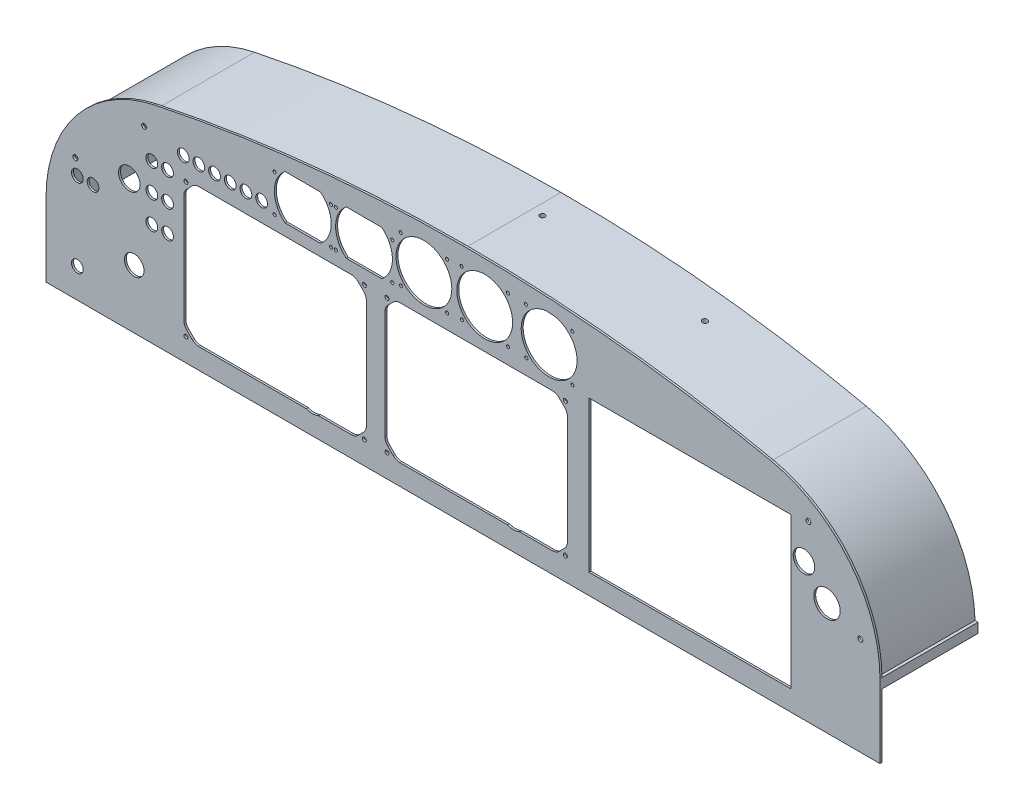
SolidWorks part; units mm, degrees
ref_plane "Front Plane" through (0, 0, 0) normal (0, 0, 1) x (1, 0, 0)
ref_plane "Top Plane" through (0, 0, 0) normal (0, 1, 0) x (1, 0, 0)
ref_plane "Right Plane" through (0, 0, 0) normal (1, 0, 0) x (0, 0, -1)
sketch "Sketch1" plane through (0, 0, 0) normal (0, 0, 1) x (1, 0, 0)
  line L7 (649.4412, 140.3074) -> (649.4412, 155.3074)
  line L9 (649.4412, 155.3074) -> (649.4412, 215.3074)
  line L39 (1500.4412, 215.3074) -> (1500.4412, 140.3074)
  line L40 (1500.4412, 140.3074) -> (649.4412, 140.3074)
  line L62 (1195.3999, 329.0734) -> (1195.3999, 146.8734) construction
  line L63 (1195.3999, 146.8734) -> (1417.5999, 146.8734) construction
  line L64 (1417.5999, 146.8734) -> (1417.5999, 329.0734) construction
  line L65 (1417.5999, 329.0734) -> (1195.3999, 329.0734) construction
  line L66 (1203.4999, 314.9734) -> (1203.4999, 160.9734)
  line L67 (1203.4999, 160.9734) -> (1409.4999, 160.9734)
  line L68 (1409.4999, 160.9734) -> (1409.4999, 314.9734)
  line L69 (1409.4999, 314.9734) -> (1203.4999, 314.9734)
  line L70 (1132.5647, 161.3083) -> (1166.0597, 161.3083)
  line L71 (1003.7003, 164.2372) -> (998.2444, 169.6931)
  line L72 (995.3155, 176.7641) -> (995.3155, 287.2524)
  line L73 (998.2444, 294.3235) -> (1003.7003, 299.7794)
  line L74 (1010.7714, 302.7083) -> (1166.0597, 302.7083)
  line L75 (1173.1307, 299.7794) -> (1178.5866, 294.3235)
  line L76 (1181.5155, 287.2524) -> (1181.5155, 176.7641)
  line L77 (1178.5866, 169.6931) -> (1173.1307, 164.2372)
  line L78 (1120.2663, 161.3083) -> (1010.7714, 161.3083)
  line L79 (989.0155, 303.7083) -> (989.0155, 160.3083) construction
  line L80 (994.0155, 155.3083) -> (1182.8155, 155.3083) construction
  line L81 (1187.8155, 160.3083) -> (1187.8155, 303.7083) construction
  line L82 (1182.8155, 308.7083) -> (994.0155, 308.7083) construction
  line L83 (927.3972, 161.3083) -> (960.8921, 161.3083)
  line L84 (798.5328, 164.2372) -> (793.0769, 169.6931)
  line L85 (790.148, 176.7641) -> (790.148, 287.2524)
  line L86 (793.0769, 294.3235) -> (798.5328, 299.7794)
  line L87 (805.6038, 302.7083) -> (960.8921, 302.7083)
  line L88 (967.9632, 299.7794) -> (973.419, 294.3235)
  line L89 (976.348, 287.2524) -> (976.348, 176.7641)
  line L90 (973.419, 169.6931) -> (967.9632, 164.2372)
  line L91 (915.0988, 161.3083) -> (805.6038, 161.3083)
  line L92 (783.848, 303.7083) -> (783.848, 160.3083) construction
  line L93 (788.848, 155.3083) -> (977.648, 155.3083) construction
  line L94 (982.648, 160.3083) -> (982.648, 303.7083) construction
  line L95 (977.648, 308.7083) -> (788.848, 308.7083) construction
  line L96 (1138.8693, 326.2789) -> (1135.2791, 322.6546)
  line L97 (1143.7303, 314.2034) -> (1147.3546, 317.7936)
  line L98 (1073.1573, 327.1493) -> (1069.5671, 323.525)
  line L99 (1078.0183, 315.0738) -> (1081.6426, 318.664)
  line L100 (1011.0893, 326.0184) -> (1007.4991, 322.3941)
  line L101 (1015.9503, 313.9429) -> (1019.5746, 317.5331)
  line L104 (955.8937, 360.0074) -> (991.9886, 360.0074)
  line L105 (955.8937, 314.6074) -> (991.9886, 314.6074)
  line L106 (893.3937, 360.0074) -> (929.4886, 360.0074)
  line L107 (893.3937, 314.6074) -> (929.4886, 314.6074)
  line L108 (670.7329, 250.3074) -> (707.3563, 250.3074) construction
  line L109 (669.6858, 170.3074) -> (692.7137, 170.3074) construction
  line L110 (724.2442, 200.3074) -> (757.1244, 200.3074) construction
  line L111 (739.7591, 245.3074) -> (779.4653, 245.3074) construction
  line L112 (745.1465, 273.3074) -> (781.6369, 273.3074) construction
  line L113 (742.3123, 301.3074) -> (779.4412, 301.3074) construction
  line L114 (779.1244, 322.3074) -> (878.3543, 322.3074) construction
  line L115 (863.5551, 337.3074) -> (1002.9412, 337.3074) construction
  line L116 (911.4412, 368.3649) -> (911.4412, 302.7083) construction
  line L117 (973.9412, 366.2956) -> (973.9412, 308.7083) construction
  line L118 (1035.0328, 379.7186) -> (1035.0328, 308.7083) construction
  line L119 (1097.1009, 379.7186) -> (1097.1009, 308.7083) construction
  line L120 (1162.8129, 379.7186) -> (1162.8129, 308.7083) construction
  line L121 (1006.5328, 341.4767) -> (1195.3999, 341.4767) construction
  circle A4 centre (853.4412, 322.3074) radius 6
  circle A48 centre (869.4412, 322.3074) radius 6
  arc A52 (649.4412, 215.3074) -> (760.4161, 352.2656) centre (789.4412, 215.3074) cw
  arc A53 (760.4161, 352.2656) -> (1074.9412, 385.3074) centre (1075.704, -1135.4566) cw
  arc A54 (1074.9412, 385.3074) -> (1389.4663, 352.2656) centre (1075.6967, -1121.0041) cw
  arc A55 (1389.4663, 352.2656) -> (1500.4412, 215.3074) centre (1360.2677, 215.1668) cw
  circle A62 centre (997.3655, 163.6583) radius 2.032
  circle A101 centre (1179.4655, 163.6583) radius 2.032
  circle A102 centre (1179.4655, 300.3583) radius 2.032
  circle A103 centre (997.3655, 300.3583) radius 2.032
  arc A104 (989.0155, 303.7083) -> (994.0155, 308.7083) centre (994.0155, 303.7083) cw construction
  arc A105 (995.3155, 287.2524) -> (998.2444, 294.3235) centre (1005.3155, 287.2524) cw
  arc A106 (1003.7003, 299.7794) -> (1010.7714, 302.7083) centre (1010.7714, 292.7083) cw
  arc A107 (995.3155, 176.7641) -> (998.2444, 169.6931) centre (1005.3155, 176.7641) ccw
  arc A108 (1003.7003, 164.2372) -> (1010.7714, 161.3083) centre (1010.7714, 171.3083) ccw
  arc A109 (989.0155, 160.3083) -> (994.0155, 155.3083) centre (994.0155, 160.3083) ccw construction
  arc A110 (1120.2663, 161.3083) -> (1132.5647, 161.3083) centre (1126.4155, 175.8083) ccw
  arc A111 (1166.0597, 161.3083) -> (1173.1307, 164.2372) centre (1166.0597, 171.3083) ccw
  arc A112 (1182.8155, 155.3083) -> (1187.8155, 160.3083) centre (1182.8155, 160.3083) ccw construction
  arc A113 (1178.5866, 169.6931) -> (1181.5155, 176.7641) centre (1171.5155, 176.7641) ccw
  arc A114 (1166.0597, 302.7083) -> (1173.1307, 299.7794) centre (1166.0597, 292.7083) cw
  arc A115 (1178.5866, 294.3235) -> (1181.5155, 287.2524) centre (1171.5155, 287.2524) cw
  arc A116 (1182.8155, 308.7083) -> (1187.8155, 303.7083) centre (1182.8155, 303.7083) cw construction
  circle A117 centre (792.198, 163.6583) radius 2.032
  circle A118 centre (974.298, 163.6583) radius 2.032
  circle A119 centre (974.298, 300.3583) radius 2.032
  circle A120 centre (792.198, 300.3583) radius 2.032
  arc A121 (783.848, 303.7083) -> (788.848, 308.7083) centre (788.848, 303.7083) cw construction
  arc A122 (790.148, 287.2524) -> (793.0769, 294.3235) centre (800.148, 287.2524) cw
  arc A123 (798.5328, 299.7794) -> (805.6038, 302.7083) centre (805.6038, 292.7083) cw
  arc A124 (790.148, 176.7641) -> (793.0769, 169.6931) centre (800.148, 176.7641) ccw
  arc A125 (798.5328, 164.2372) -> (805.6038, 161.3083) centre (805.6038, 171.3083) ccw
  arc A126 (783.848, 160.3083) -> (788.848, 155.3083) centre (788.848, 160.3083) ccw construction
  arc A127 (915.0988, 161.3083) -> (927.3972, 161.3083) centre (921.248, 175.8083) ccw
  arc A128 (960.8921, 161.3083) -> (967.9632, 164.2372) centre (960.8921, 171.3083) ccw
  arc A129 (977.648, 155.3083) -> (982.648, 160.3083) centre (977.648, 160.3083) ccw construction
  arc A130 (973.419, 169.6931) -> (976.348, 176.7641) centre (966.348, 176.7641) ccw
  arc A131 (960.8921, 302.7083) -> (967.9632, 299.7794) centre (960.8921, 292.7083) cw
  arc A132 (973.419, 294.3235) -> (976.348, 287.2524) centre (966.348, 287.2524) cw
  arc A133 (977.648, 308.7083) -> (982.648, 303.7083) centre (977.648, 303.7083) cw construction
  circle A134 centre (1162.8129, 341.7371) radius 28.5
  circle A135 centre (1139.1248, 365.4252) radius 1.6
  circle A136 centre (1186.5009, 318.049) radius 1.6
  circle A137 centre (1186.5009, 365.4252) radius 1.6
  arc A138 (1135.2791, 322.6546) -> (1143.7303, 314.2034) centre (1139.5247, 318.4489) ccw
  circle A139 centre (1097.1009, 342.6075) radius 28.5
  circle A140 centre (1073.4128, 366.2956) radius 1.6
  circle A141 centre (1120.7889, 318.9195) radius 1.6
  circle A142 centre (1120.7889, 366.2956) radius 1.6
  arc A143 (1069.5671, 323.525) -> (1078.0183, 315.0738) centre (1073.8127, 319.3194) ccw
  circle A144 centre (1035.0328, 341.4767) radius 28.5
  circle A145 centre (1011.3448, 365.1647) radius 1.6
  circle A146 centre (1058.7209, 317.7886) radius 1.6
  circle A147 centre (1058.7209, 365.1647) radius 1.6
  arc A148 (1007.4991, 322.3941) -> (1015.9503, 313.9429) centre (1011.7447, 318.1885) ccw
  circle A149 centre (789.4412, 322.3074) radius 6
  circle A150 centre (805.4412, 322.3074) radius 6
  circle A151 centre (821.4412, 322.3074) radius 6
  circle A152 centre (837.4412, 322.3074) radius 6
  circle A153 centre (1446.3342, 254.7997) radius 13.5
  circle A160 centre (945.1412, 354.3074) radius 1.6
  circle A161 centre (945.1412, 316.5574) radius 1.6
  circle A162 centre (1002.7412, 316.5574) radius 1.6
  circle A163 centre (1002.7412, 354.3074) radius 1.6
  arc A164 (991.9886, 360.0074) -> (991.9886, 314.6074) centre (973.9412, 337.3074) cw
  arc A165 (955.8937, 360.0074) -> (955.8937, 314.6074) centre (973.9412, 337.3074) ccw
  circle A166 centre (882.6376, 354.3074) radius 1.6
  circle A167 centre (882.638, 316.5574) radius 1.6
  circle A168 centre (940.2412, 316.5574) radius 1.6
  circle A169 centre (940.2412, 354.3074) radius 1.6
  arc A170 (929.4886, 360.0074) -> (929.4886, 314.6074) centre (911.4412, 337.3074) cw
  arc A171 (893.3937, 360.0074) -> (893.3937, 314.6074) centre (911.4412, 337.3074) ccw
  circle A172 centre (739.4412, 200.3074) radius 10
  circle A173 centre (757.4412, 301.3074) radius 6
  circle A174 centre (773.4412, 301.3074) radius 6
  circle A175 centre (757.4412, 273.3074) radius 6
  circle A176 centre (773.4412, 273.3074) radius 6
  circle A177 centre (757.4412, 245.3074) radius 6
  circle A178 centre (773.4653, 245.3074) radius 6
  circle A179 centre (681.4412, 250.3074) radius 6
  circle A180 centre (697.4412, 250.3074) radius 6
  circle A181 centre (681.4412, 170.3074) radius 6
  circle A182 centre (1011.7447, 318.1885) radius 1.6
  circle A183 centre (1073.8127, 319.3194) radius 1.6
  circle A184 centre (1139.5247, 318.4489) radius 1.6
  point P482 (882.4412, 337.3074)
  point P485 (944.9412, 337.3074)
  dimension "D4" = 140
  dimension "D5" = 1520.7642
  dimension "D6" = 1506.3117
  dimension "D7" = 140.1736
  dimension "D12" = 12
  dimension "D13" = 20
  dimension "D16" = 12
  dimension "D17" = 12
  dimension "D18" = 12
  dimension "D19" = 12
  dimension "D20" = 12
  dimension "D21" = 28
  dimension "D34" = 12
  dimension "D35" = 12
  dimension "D36" = 12
  dimension "D37" = 12
  dimension "D38" = 12
  dimension "D39" = 12
  dimension "D40" = 12
  dimension "D41" = 12
  dimension "D42" = 12
  dimension "D50" = 29
  dimension "D51" = 29
  dimension "D58" = 29
  dimension "D61" = 29
  dimension "D67" = 3.2
  dimension "D68" = 3.2
  dimension "D69" = 3.2
  dimension "D70" = 3.2
  dimension "D75" = 3.2
  dimension "D76" = 3.2
  dimension "D77" = 3.2
  dimension "D78" = 3.2
  dimension "D89" = 57
  dimension "D90" = 57
  dimension "D91" = 57
  dimension "D92" = 3.2
  dimension "D93" = 3.2
  dimension "D94" = 3.2
  dimension "D95" = 3.2
  dimension "D96" = 3.2
  dimension "D97" = 3.2
  dimension "D98" = 3.2
  dimension "D99" = 3.2
  dimension "D1" = 851
  dimension "D2" = 15
  dimension "D3" = 60
  dimension "D8" = 75
  dimension "D10" = 30
  dimension "D11" = 32
  dimension "D14" = 60
  dimension "D15" = 90
  dimension "D22" = 28
  dimension "D23" = 105
  dimension "D24" = 16
  dimension "D25" = 16
  dimension "D26" = 16.0242
  dimension "D28" = 108
  dimension "D29" = 108
  dimension "D30" = 108
  dimension "D31" = 32
  dimension "D32" = 16
  dimension "D33" = 110
  dimension "D43" = 16
  dimension "D44" = 16
  dimension "D45" = 16
  dimension "D46" = 16
  dimension "D47" = 16
  dimension "D48" = 182
  dimension "D49" = 140
  dimension "D52" = 45.4
  dimension "D53" = 29
  dimension "D54" = 36.0949
  dimension "D55" = 15
  dimension "D56" = 42
  dimension "D57" = 22.7
  dimension "D59" = 36.0949
  dimension "D60" = 45.4
  dimension "D62" = 62.5
  dimension "D63" = 17
  dimension "D64" = 17
  dimension "D65" = 20.75
  dimension "D66" = 20.75
  dimension "D71" = 28.8032
  dimension "D72" = 28.8
  dimension "D73" = 28.8036
  dimension "D74" = 28.8
  dimension "D79" = 22.7
  dimension "D80" = 29
  dimension "D81" = 28.8
  dimension "D82" = 28.8
  dimension "D83" = 28.8
  dimension "D84" = 28.8
  dimension "D85" = 17
  dimension "D86" = 17
  dimension "D87" = 20.75
  dimension "D88" = 20.75
  dimension "D100" = 245
  dimension "D101" = 629.0502
  dimension "D102" = 23.2882
  dimension "D103" = 23.6881
  dimension "D104" = 23.6881
  dimension "D105" = 23.6881
extrude "Boss-Extrude1" add sketch "Sketch1" along normal blind 2 contours A55 A54 A53 A52 L9 L7 L40 L39 A181 A180 A179 A178 A177 A176 A175 A174 A173 A172 A171 L106 A170 L107 A169 A168 A167 A166 A165 L104 A164 L105 A163 A162 | L98 A143 L99 A139 A183 | L100 A148 L101 A144 A182 | L96 A138 L97 A134 A184
sketch "Sketch3" plane through (0, 0, 2) normal (0, 0, 1) x (1, 0, 0)
  line L0 (679.4412, 265.3074) -> (749.4412, 328.045) construction
  line L1 (1500.4412, 140.3074) -> (649.4412, 140.3074) construction
  line L2 (1423.7763, 323.3095) -> (1484.1061, 234.9392) construction
  line L3 (674.6008, 260.9692) -> (754.2816, 332.3832) construction
  line L4 (649.4412, 140.3074) -> (649.4412, 215.3074) construction
  line L5 (1500.4412, 215.3074) -> (1500.4412, 140.3074) construction
  circle A10 centre (679.4412, 265.3074) radius 2.5
  circle A11 centre (749.4412, 328.045) radius 2.5
  circle A12 centre (734.4412, 274.3155) radius 11
  circle A13 centre (1427.4412, 317.9412) radius 2.5
  circle A14 centre (1480.4412, 240.3074) radius 2.5
  circle A15 centre (1422.8631, 280.3074) radius 11
  dimension "D3" = 5
  dimension "D10" = 125
  dimension "D11" = 100
  dimension "D16" = 73
  dimension "D17" = 20
  dimension "D20" = 22
  dimension "D7" = 5
  dimension "D8" = 5
  dimension "D12" = 5
  dimension "D19" = 22
  dimension "D24" = 140
  dimension "D4" = 94
  dimension "D5" = 107
  dimension "D6" = 6.5
  dimension "D9" = 30
  dimension "D13" = 94
  dimension "D14" = 107
  dimension "D15" = 6.5
  dimension "D18" = 100
  dimension "D21" = 30
  dimension "D22" = 15
  dimension "D23" = 25
extrude "Cut-Extrude1" cut sketch "Sketch3" against normal blind 2
sketch "Sketch4" plane through (0, 0, 2) normal (0, 0, 1) x (1, 0, 0)
  line L0 (649.4412, 215.3074) -> (689.0012, 215.3074) construction
  line L1 (760.4161, 352.2656) -> (764.1546, 347.5727) construction
  line L2 (1074.9412, 385.3074) -> (1074.9412, 379.3074) construction
  line L3 (1497.4412, 215.3074) -> (1500.4412, 215.3074)
  line L4 (1500.4412, 215.3074) -> (1462.9637, 215.3074) construction
  line L5 (649.4412, 215.3074) -> (652.4412, 215.3074)
  line L6 (649.4412, 140.3074) -> (649.4412, 215.3074) construction
  arc A1 (652.4412, 215.3074) -> (762.2854, 349.9192) centre (789.8452, 215.3074) cw
  arc A2 (762.2854, 349.9192) -> (1074.9412, 382.3074) centre (1082.1173, -1212.2508) cw
  arc A3 (1074.9412, 382.3074) -> (1386.4663, 349.2656) centre (1081.3526, -1042.327) cw
  arc A4 (1386.4663, 349.2656) -> (1497.4412, 215.3074) centre (1356.2057, 211.2504) cw
  dimension "D7" = 141.2937
  dimension "D1" = 3
  dimension "D2" = 3
  dimension "D3" = 3
  dimension "D4" = 3
  dimension "D5" = 3
  dimension "D6" = 3
extrude "Extrude-Thin1" add sketch "Sketch4" against normal blind 100 thin
ref_plane "Plane1" through (0, 0, -98) normal (0, 0, 1) x (1, 0, 0)
sketch "Sketch5" plane through (0, 0, -98) normal (0, 0, 1) x (1, 0, 0)
  line L0 (649.4412, 215.3074) -> (689.0012, 215.3074) construction
  line L3 (1497.4412, 215.3074) -> (1500.4412, 215.3074)
  line L5 (649.4412, 215.3074) -> (652.4412, 215.3074)
  arc A0 (652.4412, 215.3074) -> (726.8619, 312.2656) centre (752.812, 215.3074) cw
  arc A1 (726.8619, 312.2656) -> (1074.9412, 365.3074) centre (1140.3872, -1232.8039) cw
  arc A2 (1074.9412, 365.3074) -> (1396.9663, 312.2656) centre (1107.8718, -438.8184) cw
  arc A3 (1396.9663, 312.2656) -> (1497.4412, 215.3074) centre (1332.5921, 145.0179) cw
  dimension "D4" = 40
  dimension "D7" = 7.5
  dimension "D9" = 40
  dimension "D10" = 20
  dimension "D2" = 0
  dimension "D3" = 3
  dimension "D5" = 3
  dimension "D6" = 0
ref_plane "Plane2" through (-1.6987, 377.4622, 0) normal (-0.0045, 1, 0) x (1, 0.0045, 0)
sketch "Sketch6" plane through (-1.6987, 377.4622, 0) normal (-0.0045, 1, 0) x (1, 0.0045, 0)
  line L2 (1076.5743, 98) -> (1398.3574, 98) construction
  line L3 (1501.3949, 98) -> (1501.3949, 0) construction
  circle A2 centre (1253.4573, 68) radius 2.635
  circle A3 centre (1087.7283, 68) radius 2.6346
  dimension "D1" = 5.2692
  dimension "D2" = 5.27
  dimension "D3" = 30
  dimension "D4" = 413.6666
  dimension "D5" = 247.9376
  dimension "D6" = 30
extrude "Cut-Extrude2" cut sketch "Sketch6" against normal up to next
